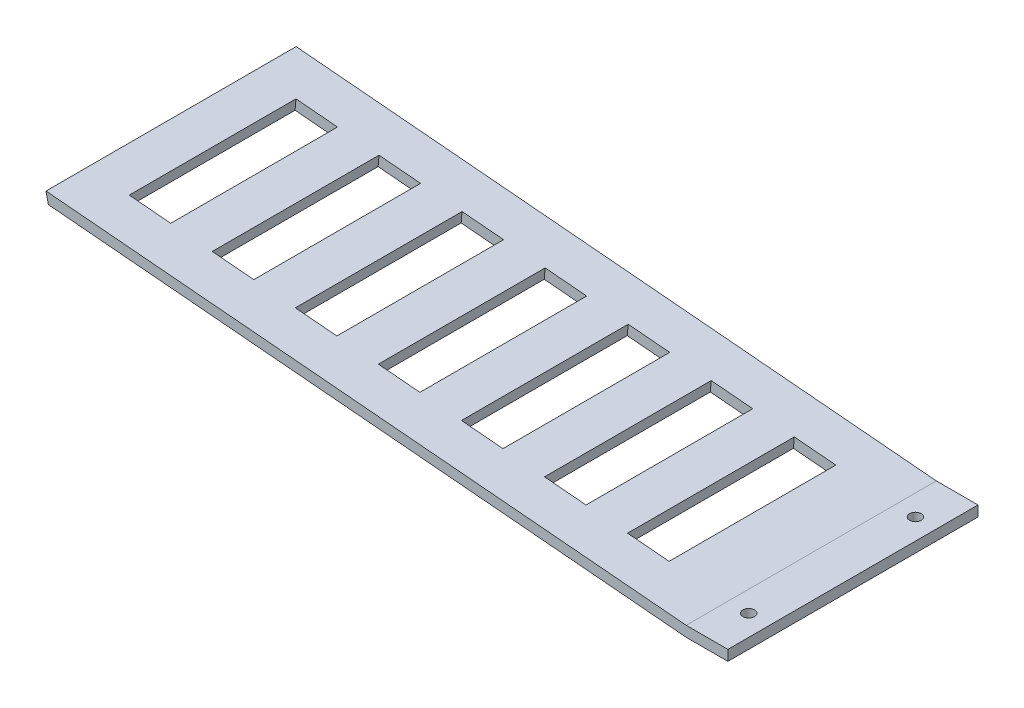
SolidWorks part; units mm, degrees
material "Copper"
ref_plane "Front Plane" through (0, 0, 0) normal (0, 0, 1) x (1, 0, 0)
ref_plane "Top Plane" through (0, 0, 0) normal (0, 1, 0) x (1, 0, 0)
ref_plane "Right Plane" through (0, 0, 0) normal (1, 0, 0) x (0, 0, -1)
sketch "Sketch1" plane through (0, 0, 0) normal (0, 0, 1) x (1, 0, 0)
  line L0 (0, 0) -> (-12.7, 0)
  line L1 (-12.7, 0) -> (-207.0095, 16.9999)
  line L5 (-207.738, 20.2386) -> (-12.7, 3.175)
  line L6 (-12.7, 3.175) -> (0, 3.175)
  line L7 (0, 3.175) -> (0, 0)
  line L8 (-207.738, 20.2386) -> (-207.0095, 16.9999)
  dimension "D1" = 3.175
  dimension "D2" = 12.7
  dimension "D3" = 12.7
  dimension "D4" = 195.0517
  dimension "D5" = 195.783
  dimension "D6" = 175
extrude "Boss-Extrude1" add sketch "Sketch1" along normal blind 76.2
sketch "Sketch2" plane through (0, 3.175, 0) normal (0, 1, 0) x (1, 0, 0)
  line L0 (0, -76.2) -> (0, 0) construction
  line L1 (0, -76.2) -> (-12.7, -76.2) construction
  circle A0 centre (-6.35, -12.7) radius 1.778
  circle A1 centre (-6.35, -63.5) radius 1.778
  dimension "D1" = 3.556
  dimension "D2" = 3.556
  dimension "D3" = 50.8
  dimension "D4" = 6.35
  dimension "D5" = 6.35
  dimension "D6" = 12.7
extrude "Cut-Extrude1" cut sketch "Sketch2" against normal blind 76.2
sketch "Sketch3" plane through (0.1792, 2.0482, 0) normal (0.0872, 0.9962, 0) x (0.9962, -0.0872, 0)
  line L0 (-12.9284, -76.2) -> (-208.7114, -76.2) construction
  line L1 (-196.0114, -12.7) -> (-183.3114, -12.7)
  line L2 (-196.0114, -12.7) -> (-196.0114, -63.5)
  line L3 (-196.0114, -63.5) -> (-183.3114, -63.5)
  line L4 (-183.3114, -12.7) -> (-183.3114, -63.5)
  line L5 (-208.7114, -76.2) -> (-208.7114, 0) construction
  dimension "D1" = 12.7
  dimension "D2" = 50.8
  dimension "D3" = 12.7
  dimension "D4" = 12.7
extrude "Cut-Extrude2" cut sketch "Sketch3" against normal blind 76.2
pattern_linear "LPattern1" count 7 spacing 25.4 along (0.9962, -0.0872, 0) of "Cut-Extrude2"
